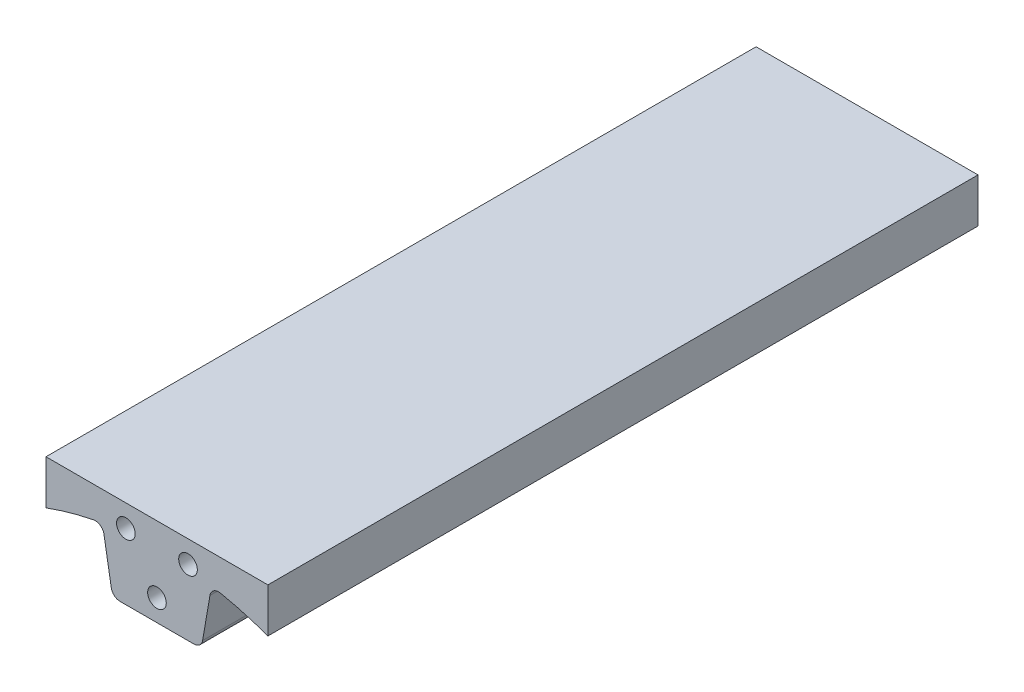
SolidWorks part; units mm, degrees
ref_plane "Front Plane" through (0, 0, 0) normal (0, 0, 1) x (1, 0, 0)
ref_plane "Top Plane" through (0, 0, 0) normal (0, 1, 0) x (1, 0, 0)
ref_plane "Right Plane" through (0, 0, 0) normal (1, 0, 0) x (0, 0, -1)
sketch "Sketch1" plane through (0, 0, 0) normal (0, 0, 1) x (1, 0, 0)
  line L0 (0, 0) -> (0, 112.4335) construction
  line L1 (-12.7, 73.8463) -> (12.7, 73.8463)
  line L2 (12.7, 73.8463) -> (15.6058, 90.7428)
  line L3 (-31.75, 99.1023) -> (31.75, 99.1023)
  line L4 (31.75, 99.1023) -> (31.75, 86.4277)
  line L5 (-31.75, 99.1023) -> (-31.75, 86.4277)
  line L6 (-12.7, 73.8463) -> (-15.6058, 90.7428)
  circle A0 centre (0, 0) radius 92.075 construction
  arc A1 (31.75, 86.4277) -> (15.6058, 90.7428) centre (0, 0) ccw
  arc A2 (-31.75, 86.4277) -> (-15.6058, 90.7428) centre (0, 0) cw
  point P12 (0, 99.1023)
  point P15 (0, 73.8463)
  dimension "D1" = 184.15
  dimension "D2" = 12.7
  dimension "D3" = 17.1446
  dimension "D4" = 31.75
  dimension "D5" = 12.6746
extrude "Boss-Extrude1" add sketch "Sketch1" along normal blind 203.2
fillet "Fillet1" radius 2.54 4 edges at (-15.6058, 90.7428, 101.6) (-12.7, 73.8463, 101.6) (12.7, 73.8463, 101.6) (15.6058, 90.7428, 101.6)
sketch "Sketch2" plane through (0, 0, 203.2) normal (0, 0, 1) x (1, 0, 0)
  line L0 (31.75, 99.1023) -> (-31.75, 99.1023) construction
  line L1 (31.75, 86.4277) -> (31.75, 99.1023) construction
  line L2 (-31.75, 99.1023) -> (-31.75, 86.4277) construction
  circle A0 centre (-8.89, 92.7523) radius 2.667
  circle A1 centre (8.89, 92.7523) radius 2.667
  circle A2 centre (0, 80.0523) radius 2.667
  dimension "D1" = 5.334
  dimension "D2" = 6.35
  dimension "D3" = 6.35
  dimension "D4" = 19.05
  dimension "D5" = 22.86
  dimension "D6" = 22.86
  dimension "D7" = 31.75
extrude "Cut-Extrude1" cut sketch "Sketch2" against normal blind 11.43 contours A2 | A1 | A0
